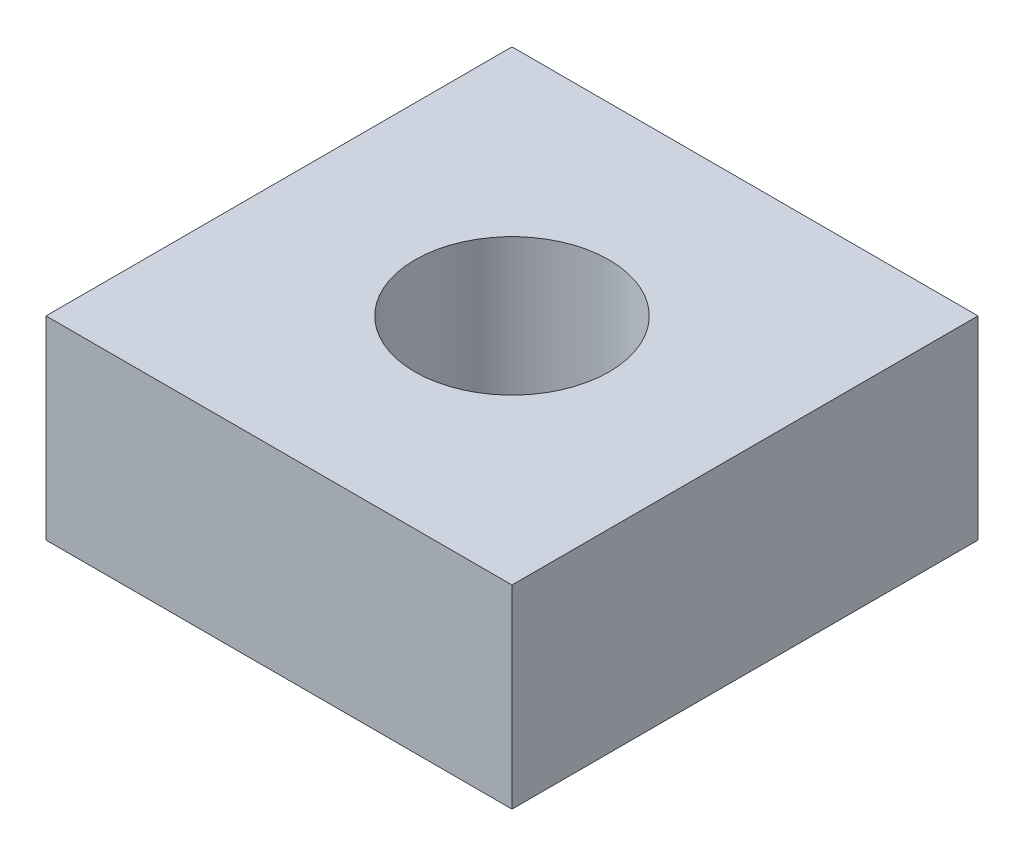
SolidWorks part; units mm, degrees
ref_plane "Front Plane" through (0, 0, 0) normal (0, 0, 1) x (1, 0, 0)
ref_plane "Top Plane" through (0, 0, 0) normal (0, 1, 0) x (1, 0, 0)
ref_plane "Right Plane" through (0, 0, 0) normal (1, 0, 0) x (0, 0, -1)
sketch "Sketch2" plane through (0, 0, 0) normal (0, 1, 0) x (1, 0, 0)
  line L1 (-60, -60) -> (60, -60)
  line L2 (-60, -60) -> (-60, 60)
  line L3 (-60, 60) -> (60, 60)
  line L4 (60, -60) -> (60, 60)
  line L5 (-60, -60) -> (60, 60) construction
  line L6 (-60, 60) -> (60, -60) construction
  point P0 (0, 0)
  dimension "D1" = 120
  dimension "D2" = 120
extrude "Boss-Extrude1" add sketch "Sketch2" along normal blind 50
sketch "Sketch3" plane through (0, 50, 0) normal (0, 1, 0) x (1, 0, 0)
  circle A0 centre (0, 0) radius 25
extrude "Cut-Extrude2" cut sketch "Sketch3" against normal through all contours A0
